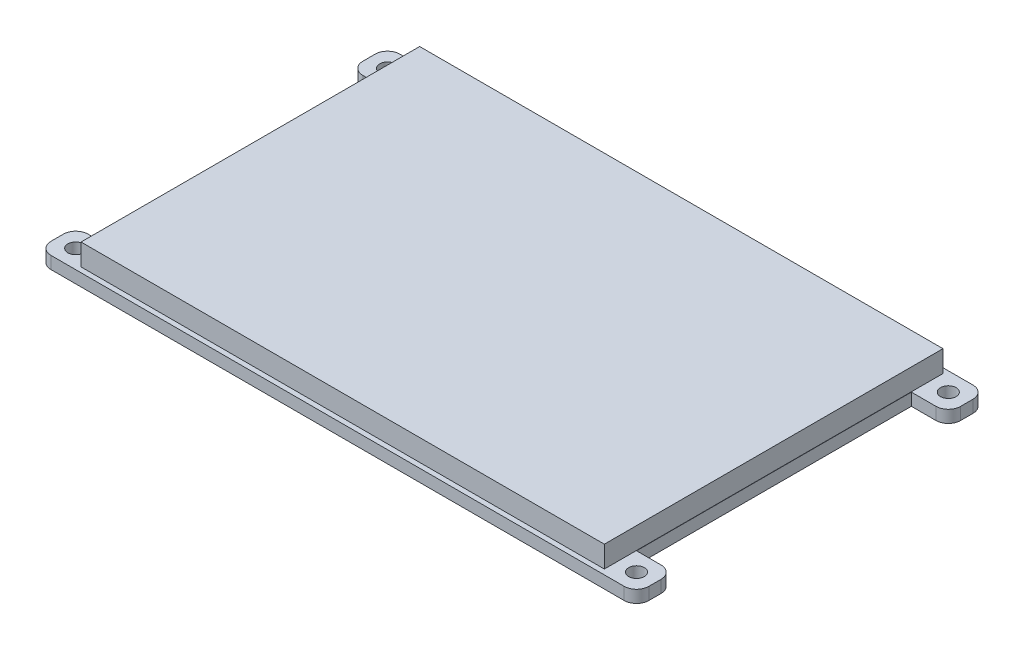
SolidWorks part; units mm, degrees
ref_plane "Front Plane" through (0, 0, 0) normal (0, 0, 1) x (1, 0, 0)
ref_plane "Top Plane" through (0, 0, 0) normal (0, 1, 0) x (1, 0, 0)
ref_plane "Right Plane" through (0, 0, 0) normal (1, 0, 0) x (0, 0, -1)
sketch "Sketch1" plane through (0, 0, 0) normal (0, 1, 0) x (1, 0, 0)
  line L1 (-42.545, 28.32) -> (42.545, 28.32)
  line L2 (-42.545, 28.32) -> (-42.545, -28.32)
  line L3 (-42.545, -28.32) -> (42.545, -28.32)
  line L4 (42.545, 28.32) -> (42.545, -28.32)
  line L5 (-42.545, 28.32) -> (42.545, -28.32) construction
  line L6 (-42.545, -28.32) -> (42.545, 28.32) construction
  point P0 (0, 0)
  dimension "D1" = 85.09
  dimension "D2" = 56.64
extrude "Boss-Extrude1" add sketch "Sketch1" along normal blind 2
sketch "Sketch3" plane through (42.545, 0, 0) normal (1, 0, 0) x (0, 0, -1)
  line L0 (-28.32, 0) -> (28.32, 0) construction
  line L1 (-28.32, 2) -> (-22.32, 2)
  line L2 (-28.32, 2) -> (-28.32, 0)
  line L3 (-28.32, 0) -> (-22.32, 0)
  line L4 (-22.32, 2) -> (-22.32, 0)
  line L5 (-28.32, 2) -> (-22.32, 0) construction
  line L6 (-28.32, 0) -> (-22.32, 2) construction
  line L7 (-28.32, 2) -> (-28.32, 0) construction
  point P0 (-25.32, 1)
  dimension "D1" = 6
  dimension "D2" = 2
  dimension "D3" = 0
extrude "Boss-Extrude4" add sketch "Sketch3" along normal blind 6
sketch "Sketch4" plane through (0, 2, 0) normal (0, 1, 0) x (1, 0, 0)
  line L0 (-42.545, -28.32) -> (48.545, -28.32) construction
  line L2 (48.545, -22.32) -> (48.545, -28.32) construction
  circle A0 centre (45.545, -25.32) radius 1.27
  dimension "D1" = 2.54
  dimension "D2" = 3
  dimension "D3" = 3
extrude "Cut-Extrude3" cut sketch "Sketch4" against normal blind 6
sketch "Sketch5" plane through (42.545, 0, 0) normal (1, 0, 0) x (0, 0, -1)
  line L0 (28.32, 2) -> (28.32, 0) construction
  line L1 (22.32, 2) -> (28.32, 2)
  line L2 (22.32, 2) -> (22.32, 0)
  line L3 (22.32, 0) -> (28.32, 0)
  line L4 (28.32, 2) -> (28.32, 0)
  line L5 (22.32, 2) -> (28.32, 0) construction
  line L6 (22.32, 0) -> (28.32, 2) construction
  line L7 (-22.32, 0) -> (28.32, 0) construction
  point P0 (25.32, 1)
  dimension "D1" = 6
  dimension "D2" = 2
extrude "Boss-Extrude5" add sketch "Sketch5" along normal blind 6
sketch "Sketch7" plane through (0, 2, 0) normal (0, 1, 0) x (1, 0, 0)
  line L0 (48.545, 22.32) -> (42.545, 22.32) construction
  line L1 (48.545, 28.32) -> (48.545, 22.32) construction
  circle A0 centre (45.545, 25.32) radius 1.27
  dimension "D1" = 2.54
  dimension "D2" = 3
  dimension "D3" = 3
extrude "Cut-Extrude4" cut sketch "Sketch7" against normal blind 6
sketch "Sketch8" plane through (-42.545, 0, 0) normal (-1, 0, 0) x (0, 0, 1)
  line L0 (-28.32, 0) -> (28.32, 0) construction
  line L1 (-28.32, 2) -> (-22.32, 2)
  line L2 (-28.32, 2) -> (-28.32, 0)
  line L3 (-28.32, 0) -> (-22.32, 0)
  line L4 (-22.32, 2) -> (-22.32, 0)
  line L5 (-28.32, 2) -> (-22.32, 0) construction
  line L6 (-28.32, 0) -> (-22.32, 2) construction
  line L7 (-28.32, 2) -> (-28.32, 0) construction
  point P0 (-25.32, 1)
  dimension "D1" = 6
  dimension "D2" = 2
  dimension "D3" = 0
extrude "Boss-Extrude6" add sketch "Sketch8" along normal blind 6
sketch "Sketch9" plane through (-42.545, 0, 0) normal (-1, 0, 0) x (0, 0, 1)
  line L1 (22.32, 2) -> (28.32, 2)
  line L2 (22.32, 2) -> (22.32, 0)
  line L3 (22.32, 0) -> (28.32, 0)
  line L4 (28.32, 2) -> (28.32, 0)
  line L5 (22.32, 2) -> (28.32, 0) construction
  line L6 (22.32, 0) -> (28.32, 2) construction
  point P0 (25.32, 1)
  dimension "D1" = 6
  dimension "D2" = 2
extrude "Boss-Extrude7" add sketch "Sketch9" along normal blind 6
sketch "Sketch10" plane through (0, 2, 0) normal (0, 1, 0) x (1, 0, 0)
  line L0 (48.545, 28.32) -> (-48.545, 28.32) construction
  line L1 (-48.545, 22.32) -> (-48.545, 28.32) construction
  circle A0 centre (-45.545, 25.32) radius 1.27
  dimension "D1" = 2.54
  dimension "D2" = 3
  dimension "D3" = 3
extrude "Cut-Extrude5" cut sketch "Sketch10" against normal blind 6
sketch "Sketch11" plane through (0, 2, 0) normal (0, 1, 0) x (1, 0, 0)
  line L0 (-48.545, -22.32) -> (-42.545, -22.32) construction
  line L1 (-48.545, -28.32) -> (-48.545, -22.32) construction
  circle A0 centre (-45.545, -25.32) radius 1.27
  dimension "D1" = 2.54
  dimension "D2" = 3
  dimension "D3" = 3
extrude "Cut-Extrude6" cut sketch "Sketch11" against normal blind 6
fillet "Fillet5" radius 2 8 edges at (48.545, 1, 28.32) (48.545, 1, 22.32) (48.545, 1, -28.32) (48.545, 1, -22.32) (-48.545, 1, -28.32) (-48.545, 1, -22.32) (-48.545, 1, 28.32) (-48.545, 1, 22.32)
sketch "Sketch12" plane through (0, 0, 0) normal (0, -1, 0) x (1, 0, 0)
  line L0 (46.545, -28.32) -> (-46.545, -28.32) construction
  line L1 (-41.545, -22.12) -> (-8.045, -22.12)
  line L2 (-41.545, -22.12) -> (-41.545, -27.32)
  line L3 (-41.545, -27.32) -> (-8.045, -27.32)
  line L4 (-8.045, -22.12) -> (-8.045, -27.32)
  line L5 (-41.545, -22.12) -> (-8.045, -27.32) construction
  line L6 (-41.545, -27.32) -> (-8.045, -22.12) construction
  line L7 (-42.545, -22.32) -> (-42.545, 22.32) construction
  point P0 (-24.795, -24.72)
  dimension "D1" = 33.5
  dimension "D2" = 5.2
  dimension "D3" = 1
  dimension "D4" = 1
extrude "Boss-Extrude8" add sketch "Sketch12" along normal blind 15
sketch "Sketch14" plane through (0, -15, 0) normal (0, -1, 0) x (1, 0, 0)
  line L0 (-8.045, -22.12) -> (-41.545, -22.12) construction
  line L1 (-41.545, -22.22) -> (-8.145, -22.22)
  line L2 (-41.545, -22.22) -> (-41.545, -27.22)
  line L3 (-41.545, -27.22) -> (-8.145, -27.22)
  line L4 (-8.145, -22.22) -> (-8.145, -27.22)
  line L5 (-41.545, -22.22) -> (-8.145, -27.22) construction
  line L6 (-41.545, -27.22) -> (-8.145, -22.22) construction
  line L7 (-41.545, -22.12) -> (-41.545, -27.32) construction
  point P0 (-24.845, -24.72)
  dimension "D1" = 33.4
  dimension "D2" = 5
  dimension "D3" = 0.1
  dimension "D4" = 0
extrude "Cut-Extrude9" cut sketch "Sketch14" against normal blind 6
sketch "Sketch15" plane through (0, 0, 0) normal (0, -1, 0) x (1, 0, 0)
  line L0 (-46.545, 28.32) -> (46.545, 28.32) construction
  line L1 (-34.545, 17.32) -> (-39.545, 17.32)
  line L2 (-34.545, 17.32) -> (-34.545, -15.68)
  line L3 (-34.545, -15.68) -> (-39.545, -15.68)
  line L4 (-39.545, 17.32) -> (-39.545, -15.68)
  line L5 (-34.545, 17.32) -> (-39.545, -15.68) construction
  line L6 (-34.545, -15.68) -> (-39.545, 17.32) construction
  line L7 (-42.545, -22.32) -> (-42.545, 22.32) construction
  point P0 (-37.045, 0.82)
  dimension "D1" = 33
  dimension "D2" = 5
  dimension "D3" = 11
  dimension "D4" = 3
extrude "Boss-Extrude9" add sketch "Sketch15" along normal blind 9
sketch "Sketch16" plane through (0, 2, 0) normal (0, 1, 0) x (1, 0, 0)
  line L1 (42.5, 27.5) -> (-42.5, 27.5)
  line L2 (42.5, 27.5) -> (42.5, -27.5)
  line L3 (42.5, -27.5) -> (-42.5, -27.5)
  line L4 (-42.5, 27.5) -> (-42.5, -27.5)
  line L5 (42.5, 27.5) -> (-42.5, -27.5) construction
  line L6 (42.5, -27.5) -> (-42.5, 27.5) construction
  point P0 (0, 0)
  dimension "D1" = 85
  dimension "D2" = 55
extrude "Boss-Extrude10" add sketch "Sketch16" along normal blind 3.5
